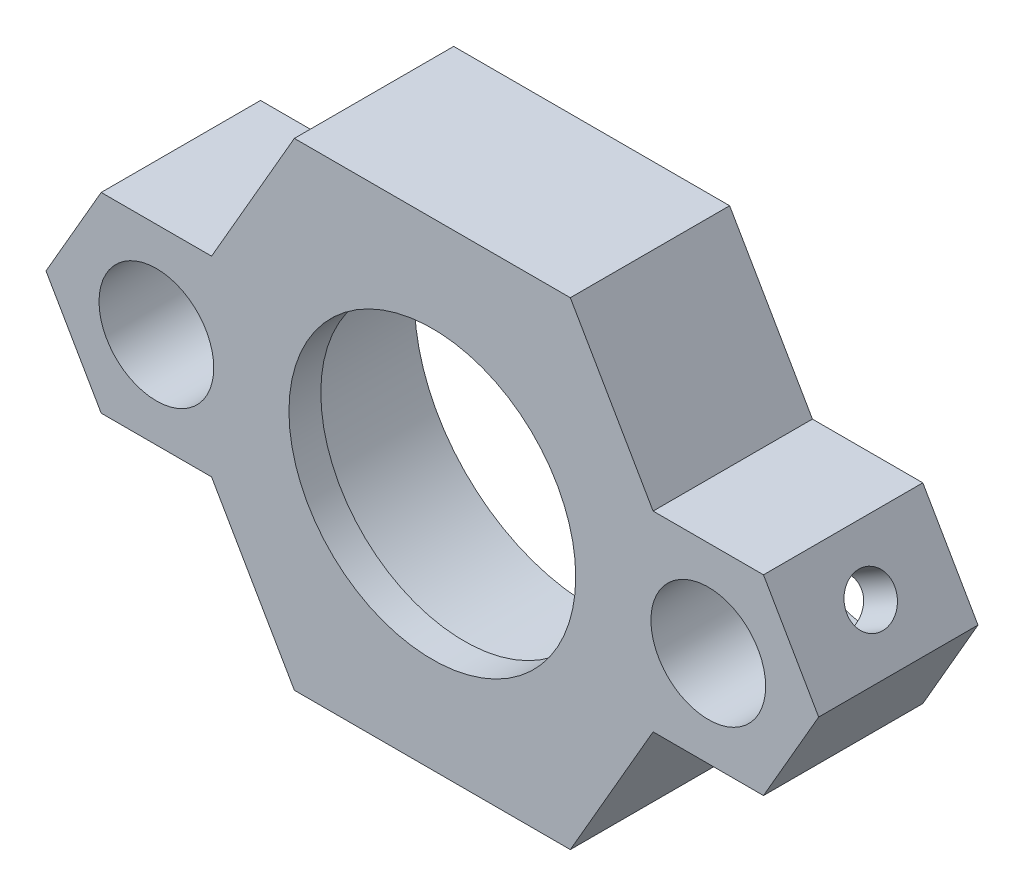
SolidWorks part; units mm, degrees
ref_plane "Front Plane" through (0, 0, 0) normal (0, 0, 1) x (1, 0, 0)
ref_plane "Top Plane" through (0, 0, 0) normal (0, 1, 0) x (1, 0, 0)
ref_plane "Right Plane" through (0, 0, 0) normal (1, 0, 0) x (0, 0, -1)
sketch "Sketch3" plane through (0, 0, 0) normal (0, 0, 1) x (1, 0, 0)
  line L0 (-15, 0) -> (17.3205, 0) construction
  line L1 (17.3205, 0) -> (15.5205, 3.1177) construction
  line L2 (8.6603, 15) -> (-8.6603, 15)
  line L3 (-8.6603, 15) -> (-13.8564, 6)
  line L4 (-13.8564, -6) -> (-8.6603, -15)
  line L5 (-8.6603, -15) -> (8.6603, -15)
  line L6 (8.6603, -15) -> (13.8564, -6)
  line L7 (0, 15) -> (0, -15) construction
  line L8 (24.2487, 0) -> (20.7846, 6)
  line L9 (20.7846, 6) -> (13.8564, 6)
  line L10 (12.1244, 3) -> (11.064, 1.1634) construction
  line L11 (11.064, -1.1634) -> (12.1244, -3) construction
  line L12 (13.8564, -6) -> (20.7846, -6)
  line L13 (20.7846, -6) -> (24.2487, 0)
  line L14 (-20.7846, -6) -> (-24.2487, 0)
  line L15 (-13.8564, -6) -> (-20.7846, -6)
  line L16 (-11.064, -1.1634) -> (-13.8564, -6) construction
  line L17 (-11.064, 1.1634) -> (-10.3923, 0) construction
  line L18 (-20.7846, 6) -> (-13.8564, 6)
  line L19 (-24.2487, 0) -> (-20.7846, 6)
  line L20 (-15.5205, 3.1177) -> (-17.3205, 0) construction
  line L21 (-17.3205, 0) -> (-15, 0) construction
  line L22 (-17.3205, 0) -> (-15.5205, -3.1177) construction
  line L23 (-13.8564, 6) -> (-15.5205, 3.1177) construction
  line L24 (-15.5205, -3.1177) -> (-13.8564, -6) construction
  line L25 (15.5205, 3.1177) -> (14.3205, 5.1962) construction
  line L26 (13.8564, 6) -> (8.6603, 15)
  line L27 (15.5205, -3.1177) -> (17.3205, 0) construction
  line L28 (14.3205, -5.1962) -> (15.5205, -3.1177) construction
  line L29 (13.8564, -6) -> (14.3205, -5.1962) construction
  line L30 (14.3205, 5.1962) -> (13.8564, 6) construction
  line L31 (-13.8564, 6) -> (-11.064, 1.1634) construction
  line L32 (-10.3923, 0) -> (-11.064, -1.1634) construction
  line L33 (12.1244, -3) -> (13.8564, -6) construction
  line L34 (10.3923, 0) -> (11.064, -1.1634) construction
  line L35 (11.064, 1.1634) -> (10.3923, 0) construction
  line L36 (13.8564, 6) -> (12.1244, 3) construction
  circle A0 centre (0, 0) radius 11.125
  circle A1 centre (0, 0) radius 15 construction
  circle A2 centre (17.3205, 0) radius 3.6
  circle A3 centre (17.3205, 0) radius 6 construction
  circle A4 centre (-17.3205, 0) radius 3.6
  dimension "D1" = 22.25
  dimension "D3" = 7.2
  dimension "D2" = 30
  dimension "D4" = 12
extrude "Boss-Extrude1" add sketch "Sketch3" along normal blind 8
sketch "Sketch4" plane through (0, 0, 8) normal (0, 0, 1) x (1, 0, 0)
  line L0 (-8.6603, 15) -> (-13.8564, 6)
  line L1 (-13.8564, 6) -> (-20.7846, 6)
  line L2 (-20.7846, 6) -> (-24.2487, 0)
  line L3 (-24.2487, 0) -> (-20.7846, -6)
  line L4 (-20.7846, -6) -> (-13.8564, -6)
  line L5 (-13.8564, -6) -> (-8.6603, -15)
  line L6 (-8.6603, -15) -> (8.6603, -15)
  line L7 (8.6603, -15) -> (13.8564, -6)
  line L8 (13.8564, -6) -> (20.7846, -6)
  line L9 (20.7846, -6) -> (24.2487, 0)
  line L10 (24.2487, 0) -> (20.7846, 6)
  line L11 (20.7846, 6) -> (13.8564, 6)
  line L12 (13.8564, 6) -> (8.6603, 15)
  line L13 (8.6603, 15) -> (-8.6603, 15)
  circle A0 centre (0, 0) radius 9
  circle A1 centre (-17.3205, 0) radius 3.6
  circle A2 centre (17.3205, 0) radius 3.6
  circle A3 centre (-17.3205, 0) radius 3.6 construction
  circle A4 centre (17.3205, 0) radius 3.6 construction
  dimension "D1" = 18
extrude "Boss-Extrude3" add sketch "Sketch4" along normal blind 2
sketch "Sketch5" plane through (-18.1865, 10.5, 0) normal (-0.866, 0.5, 0) x (0, 0, 1)
  line L0 (5, -5.1962) -> (5, -12.1244) construction
  line L1 (10, -5.1962) -> (0, -5.1962) construction
  line L2 (10, -12.1244) -> (0, -12.1244) construction
  line L3 (0, -8.6603) -> (10, -8.6603) construction
  line L4 (0, -5.1962) -> (0, -12.1244) construction
  circle A0 centre (5, -8.6603) radius 1.5
  dimension "D1" = 3
extrude "Cut-Extrude1" cut sketch "Sketch5" against normal up to surface (2.7274 mm away)
sketch "Sketch6" plane through (18.1865, 10.5, 0) normal (0.866, 0.5, 0) x (0, 0, -1)
  line L0 (-5, -5.1962) -> (-5, -12.1244) construction
  line L1 (-10, -5.1962) -> (0, -5.1962) construction
  line L2 (-10, -12.1244) -> (0, -12.1244) construction
  line L3 (-10, -8.6603) -> (0, -8.6603) construction
  line L4 (-10, -12.1244) -> (-10, -5.1962) construction
  line L5 (0, -12.1244) -> (0, -5.1962) construction
  circle A0 centre (-5, -8.6603) radius 1.5
  dimension "D1" = 3
extrude "Cut-Extrude2" cut sketch "Sketch6" against normal up to surface (2.7274 mm away)
